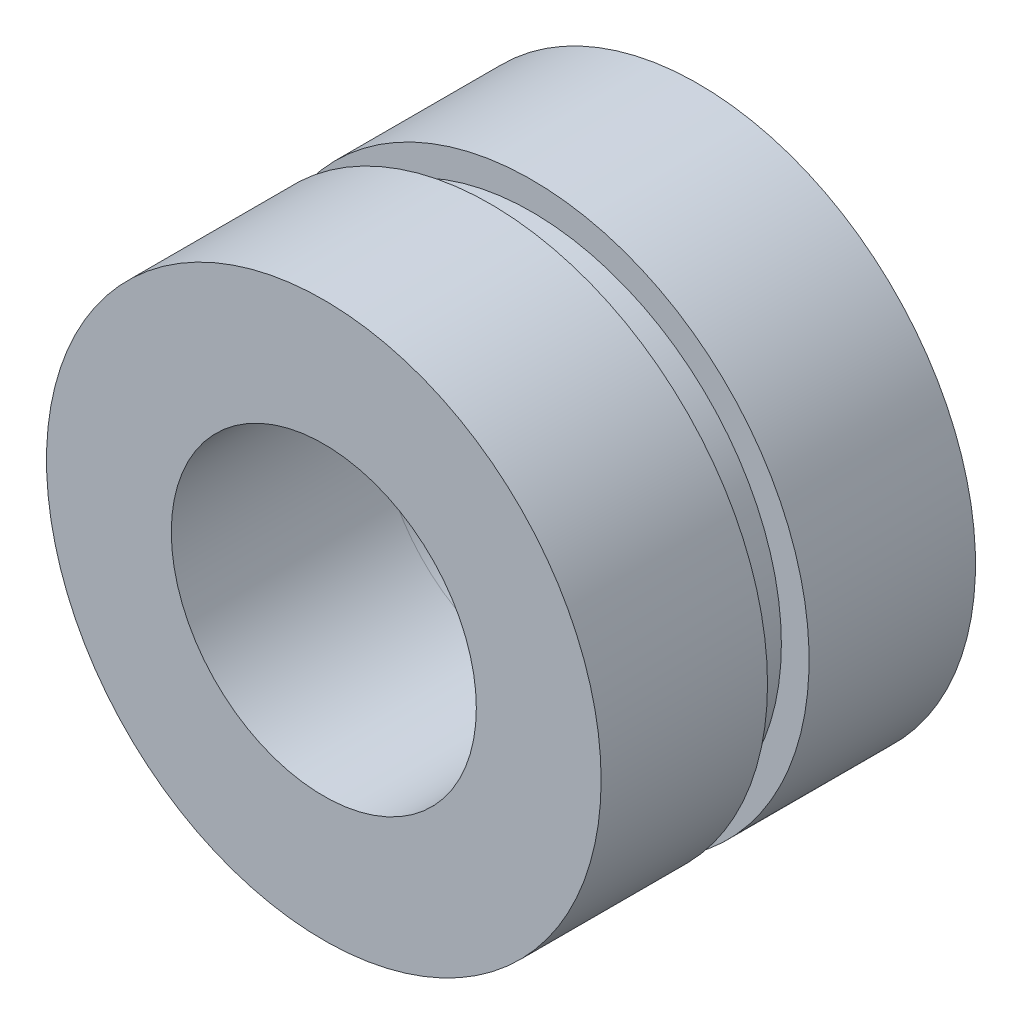
SolidWorks part; units mm, degrees
ref_plane "Front Plane" through (0, 0, 0) normal (0, 0, 1) x (1, 0, 0)
ref_plane "Top Plane" through (0, 0, 0) normal (0, 1, 0) x (1, 0, 0)
ref_plane "Right Plane" through (0, 0, 0) normal (1, 0, 0) x (0, 0, -1)
sketch "Sketch1" plane through (0, 0, 0) normal (0, 0, 1) x (1, 0, 0)
  circle A0 centre (0, 0) radius 2.794
  circle A1 centre (0, 0) radius 4.572
  dimension "D1" = 1.778
  dimension "D2" = 5.588
extrude "Boss-Extrude2" add sketch "Sketch1" along normal blind 0.762 contours A1
sketch "Sketch3" plane through (0, 0, 0.762) normal (0, 0, 1) x (1, 0, 0)
  circle A0 centre (0, 0) radius 2.794
  circle A1 centre (0, 0) radius 5.08
  dimension "D1" = 2.286
  dimension "D2" = 5.588
extrude "Boss-Extrude3" add sketch "Sketch3" along normal blind 3.048
sketch "Sketch4" plane through (0, 0, 0) normal (0, 0, -1) x (-1, 0, 0)
  circle A0 centre (0, 0) radius 2.794
  circle A1 centre (0, 0) radius 5.08
  dimension "D1" = 5.588
  dimension "D2" = 10.16
extrude "Boss-Extrude4" add sketch "Sketch4" along normal blind 3.048 separate body
